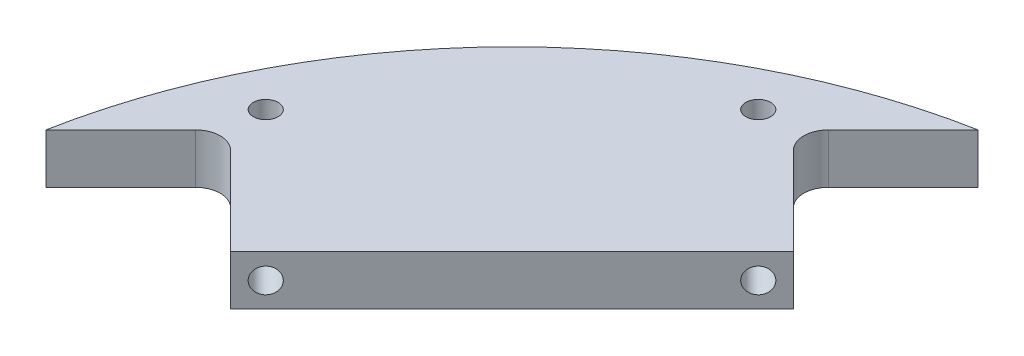
SolidWorks part; units mm, degrees
material "6061-T6 (SS)"
ref_plane "Front Plane" through (0, 0, 0) normal (0, 0, 1) x (1, 0, 0)
ref_plane "Top Plane" through (0, 0, 0) normal (0, 1, 0) x (1, 0, 0)
ref_plane "Right Plane" through (0, 0, 0) normal (1, 0, 0) x (0, 0, -1)
sketch "Constraints" plane through (0, 0, 0) normal (0, 1, 0) x (1, 0, 0)
  line L0 (0, 152.4) -> (0, -152.4) construction
  line L1 (-152.4, 0) -> (152.4, 0) construction
  circle A0 centre (0, 0) radius 152.4 construction
  circle A1 centre (0, 0) radius 149.225 construction
  circle A2 centre (0, 0) radius 12.7 construction
  circle A3 centre (0, 76.454) radius 12.7 construction
  circle A4 centre (76.454, 0) radius 12.7 construction
  circle A5 centre (0, -76.454) radius 12.7 construction
  circle A6 centre (-76.454, 0) radius 12.7 construction
  point P20 (0, 0)
  dimension "D1" = 25.4
  dimension "D4" = 304.8
  dimension "D3" = 76.454
  dimension "D2" = 3.175
  dimension "D6" = 76.454
  dimension "D7" = 76.454
  dimension "D5" = 4
sketch "Base" plane through (0, 0, 0) normal (0, 1, 0) x (1, 0, 0)
  line L0 (0, 76.454) -> (-76.454, 0) construction
  line L5 (21.8789, -21.8789) -> (-16.3481, 16.3481) construction
  line L9 (-27.6819, 146.635) -> (-51.2374, 123.0795)
  line L14 (-24.2966, 96.1387) -> (-51.2374, 123.0795)
  line L15 (-146.635, 27.6819) -> (-123.0795, 51.2374)
  line L16 (-96.1387, 24.2966) -> (-123.0795, 51.2374)
  line L18 (-19.5371, 78.1962) -> (-81.4004, 16.3329) construction
  line L19 (-24.2966, 96.1387) -> (-96.1387, 24.2966)
  arc A2 (-146.635, 27.6819) -> (-27.6819, 146.635) centre (0, 0) cw
  circle A3 centre (0, 0) radius 149.225 construction
  point P18 (-96.1387, 96.1387)
  dimension "D4" = 38.1
  dimension "D1" = 68.619
extrude "Cradle" add sketch "Base" along normal blind 12.7 contours L9 L14 L19 L16 L15 A2
ref_plane "Mirror Plane 1" through (0, 6.35, 0) normal (0, 1, 0) x (1, 0, 0)
sketch "Sketch1" plane through (0, 12.7, 0) normal (0, 1, 0) x (1, 0, 0)
  line L0 (-51.2374, 123.0795) -> (-69.1979, 123.0795) construction
  line L3 (-60.2177, 60.2177) -> (-78.9078, 78.9078) construction
  line L5 (-24.2966, 96.1387) -> (-51.2374, 123.0795) construction
  line L6 (-24.2966, 96.1387) -> (-96.1387, 24.2966) construction
  circle A0 centre (-60.2177, 123.0795) radius 3.175
  circle A1 centre (-123.0795, 60.2177) radius 3.175
  point P2 (-60.2177, 123.0795)
  point P18 (-60.2177, 60.2177)
  dimension "D1" = 6.35
  dimension "D2" = 17.9605
extrude "Cut-Extrude1" cut sketch "Sketch1" against normal blind 12.7 contours A0 | A1
ref_plane "Mirror Plane 2" through (0, 0, 0) normal (0.7071, 0, -0.7071) x (-0.7071, 0, -0.7071)
fillet "Quarter Inch Fillets" radius 6.35 2 edges at (-123.0795, 6.35, -51.2374) (-51.2374, 6.35, -123.0795)
sketch "Sketch4" plane through (-60.2177, 0, -60.2177) normal (0.7071, 0, 0.7071) x (0.7071, 0, -0.7071)
  line L0 (50.8, 12.7) -> (-50.8, 12.7) construction
  line L1 (50.8, 0) -> (38.1, 0)
  line L2 (50.8, 0) -> (50.8, 12.7)
  line L3 (50.8, 12.7) -> (38.1, 12.7)
  line L4 (38.1, 0) -> (38.1, 12.7) construction
  line L5 (50.8, 0) -> (38.1, 12.7) construction
  line L6 (50.8, 0) -> (-50.8, 0) construction
  line L7 (0, 0) -> (0, 12.7) construction
  circle A0 centre (44.45, 6.35) radius 3.175
  circle A1 centre (-44.45, 6.35) radius 3.175
  dimension "D1" = 6.35
extrude "0.25\"-28 Diameter Tapped Holes for Lid" cut sketch "Sketch4" against normal blind 12.7 contours A0 | A1
equation "\"Pipe Diameter\"= 1in"
equation "\"D1@Constraints\"=\"Pipe Diameter\""
equation "\"Pipe Radial Distance\"= 3.01in"
equation "\"D3@Constraints\"=\"Pipe Radial Distance\""
equation "\"Rocket Diameter\"= 12in"
equation "\"D4@Constraints\"=\"Rocket Diameter\""
equation "\"Airframe Thickness\"= 0.125in"
equation "\"D2@Constraints\"=\"Airframe Thickness\""
equation "\"D6@Constraints\"=\"Pipe Radial Distance\""
equation "\"D7@Constraints\"=\"Pipe Radial Distance\""
equation "\"Arduino Mega Length\"= 101.52mm"
equation "\"Arduino Mega Width\"= 53.3mm"
equation "\"Interior Height\"= 2in"
equation "\"Wall Thickness\"= 0.5in"
equation "\"Assembly Hole Diameter\"= 0.25in"
equation "\"D4@Base\" = \"Interior Height\" - \"Wall Thickness\""
equation "\"4-40 Standoff Depth\"= 0.1875in"
equation "\"D1@Cradle\"=\"Wall Thickness\""
equation "\"D1@Sketch1\"=\"Assembly Hole Diameter\""
equation "\"D1@Cut-Extrude1\"=\"Wall Thickness\""
equation "\"Wire Hole Diameter\"= 0.1in"
equation "\"D1@Sketch4\"=\"Assembly Hole Diameter\""
